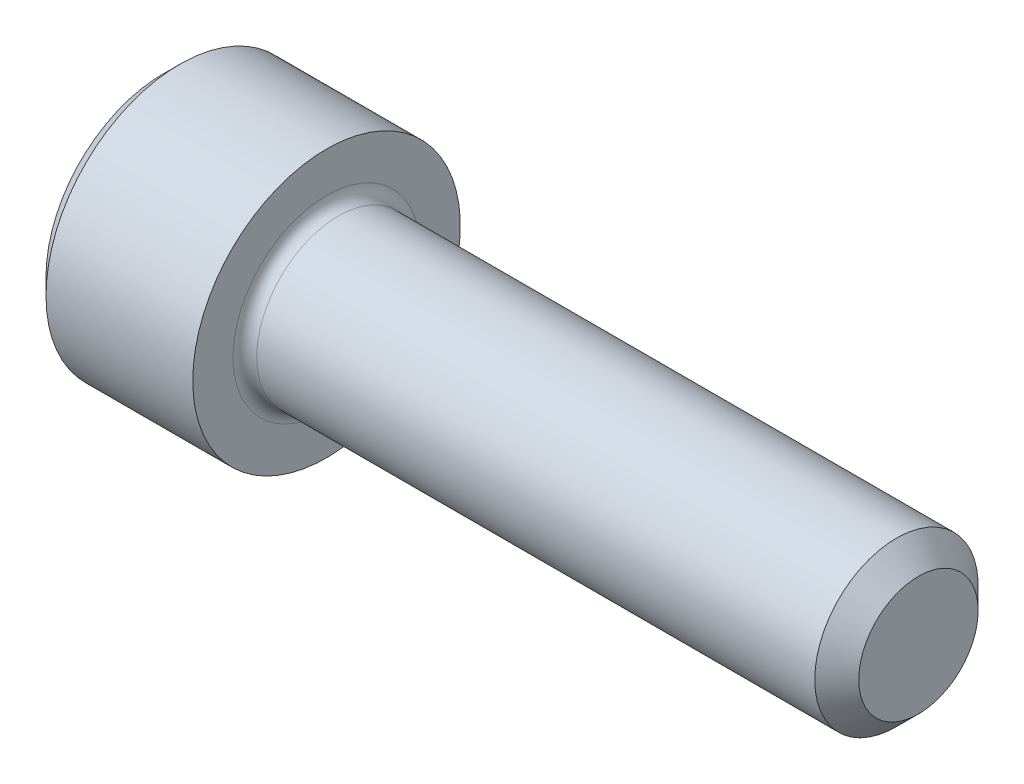
SolidWorks part; units mm, degrees
material "Alloy Steel"
ref_plane "Plane1" through (0, 0, 0) normal (0, 0, 1) x (1, 0, 0)
ref_plane "Plane2" through (0, 0, 0) normal (0, 1, 0) x (1, 0, 0)
ref_plane "Plane3" through (0, 0, 0) normal (1, 0, 0) x (0, 0, -1)
sketch "BodySke" plane through (0, 0, 0) normal (0, 0, 1) x (1, 0, 0)
  line L0 (0, 0) -> (0, 2.5146)
  line L1 (0.3556, 2.8702) -> (3.5052, 2.8702)
  line L2 (3.5052, 2.8702) -> (3.5052, 1.7526)
  line L3 (3.5052, 1.7526) -> (15.7328, 1.7526)
  line L4 (16.2052, 1.2802) -> (16.2052, 0)
  line L5 (16.2052, 0) -> (0, 0)
  line L6 (-31.75, 0) -> (127, 0) construction
  line L7 (0, 2.5146) -> (0.3556, 2.8702)
  line L8 (16.2052, 1.2802) -> (15.7328, 1.7526)
  line L9 (0, -2.5146) -> (0.3556, -2.8702) construction
  line L10 (16.2052, -1.2802) -> (15.7328, -1.7526) construction
  line L11 (4.2977, 9.525) -> (4.2977, 3.175) construction
  line L12 (3.5052, 9.525) -> (3.5052, 3.175) construction
  line L13 (-21.8948, 9.525) -> (-21.8948, 3.175) construction
  dimension "Diameter" = 3.5052
  dimension "Head_ht" = 3.5052
  dimension "Length" = 12.7
  dimension "Body_ch_ang" = 45
  dimension "Head_dia" = 5.7404
  dimension "Head_ch_ang" = 45
  dimension "Head_side_ht" = 3.1496
  dimension "Minor_dia" = 2.5603
  dimension "Advance" = 0.7925
  dimension "Thread_nom" = 12.7
  dimension "Thread_length" = 38.1
revolve "Base-Revolve" add sketch "BodySke"
cosmetic thread "ThreadCosmetic"
fillet "Fillet1" radius 0.254 1 edges at (3.5052, 0, 1.7526)
sketch "Sketch2" plane through (0, 0, 0) normal (0, 0, 1) x (1, 0, 0)
  line L0 (0, 1.3843) -> (1.6256, 1.3843)
  line L1 (1.6256, 1.3843) -> (2.4248, 0)
  line L2 (-31.75, 0) -> (127, 0) construction
  line L3 (2.4248, 0) -> (0, 0)
  line L4 (0, 0) -> (0, 1.3843)
  line L5 (0, 2.5146) -> (0, -2.5146) construction
  line L6 (0, 0) -> (47.625, 0) construction
  line L7 (3.5052, -2.8702) -> (3.5052, 2.8702) construction
  dimension "D1" = 1.3843
  dimension "D2" = 60
  dimension "Wall_thickness" = 1.8796
revolve "Hex-PreBroach" cut sketch "Sketch2" angle 360 about L6
sketch "Sketch3" plane through (0, 0, 0) normal (-1, 0, 0) x (0, 0.5, 0.866)
  line L0 (0.7992, 1.3843) -> (-0.7992, 1.3843)
  line L1 (-0.7992, 1.3843) -> (-1.5985, 0)
  line L2 (0.7992, 1.3843) -> (1.5985, 0)
  line L3 (0.7992, -1.3843) -> (1.5985, 0)
  line L4 (0.7992, -1.3843) -> (-0.7992, -1.3843)
  line L5 (-0.7992, -1.3843) -> (-1.5985, 0)
  dimension "D1" = 1.3843
  dimension "D2" = 1.3843
  dimension "Hex_size" = 2.7686
extrude "Hex" cut sketch "Sketch3" against normal blind 1.6256
sketch "Sketch4" plane through (0, 0, 0) normal (-1, 0, 0) x (0, 0, 1)
  line L0 (0, 0) -> (1.7399, 0)
  line L1 (0, 0) -> (6.1484, 3.5498) construction
  line L2 (0, 0) -> (0.8699, 1.5068)
  line L3 (1.4457, 0.3947) -> (1.6607, 0.5189)
  line L4 (1.0647, 1.0546) -> (1.2797, 1.1788)
  arc A0 (1.4457, 0.3947) -> (1.0647, 1.0546) centre (0, 0) ccw
  arc A1 (1.7399, 0) -> (1.6607, 0.5189) centre (0, 0) ccw
  arc A2 (0.8699, 1.5068) -> (1.2797, 1.1788) centre (0, 0) cw
  dimension "D1" = 30
  dimension "Spline_n_dim" = 2.9972
  dimension "Spline_m_dim" = 3.4798
  dimension "D2" = 60
  dimension "D3" = 0.381
  dimension "Spline_p_dim" = 0.762
extrude "Spline" [suppressed] cut sketch "Sketch4" against normal blind 1.6256
pattern_circular "CirPattern1" [suppressed] count 6 every 60
sketch "Sketch5" plane through (0, 0, 0) normal (0, 0, 1) x (1, 0, 0)
  line L0 (-31.75, 0) -> (127, 0) construction
  line L2 (0, 2.5146) -> (0, -2.5146) construction
  circle A0 centre (1.27, 0) radius 0.4445
  dimension "Drilled_hole_dia" = 0.889
  dimension "Drilled_hole_loc" = 1.27
extrude "Hole" [suppressed] cut sketch "Sketch5" against normal through all and the other way through all
pattern_circular "Drilled-4" [suppressed] count 2 every 60
pattern_circular "Drilled-6" [suppressed] count 3 every 60
sketch "ThdSchSke" plane through (0, 0, 0) normal (0, 0, 1) x (1, 0, 0)
  line L0 (4.2977, -1.2802) -> (3.9669, -1.7526)
  line L1 (4.2977, -1.2802) -> (4.6285, -1.7526)
  line L2 (4.6285, -1.7526) -> (4.6285, -2.1908)
  line L3 (-3.175, 0) -> (5.1513, 0) construction
  line L5 (4.6285, -2.1908) -> (3.9669, -2.1908)
  line L6 (3.9669, -2.1908) -> (3.9669, -1.7526)
  line L7 (0, 2.5146) -> (0, -2.5146) construction
  dimension "Thread_minor" = 2.5603
  dimension "Diameter" = 3.5052
  dimension "Start" = 4.2977
  dimension "SideAngle" = 55
  dimension "VeeAngle" = 70
  dimension "Overcut" = 4.3815
revolve "ThreadSchematic" [suppressed] cut sketch "ThdSchSke" angle 360 about L3
pattern_linear "ThdSchPat" [suppressed]
equation "\"D2@Sketch3\" = \"Hex_size@Sketch3\" / 2"
equation "\"D1@Sketch3\" = \"Hex_size@Sketch3\" / 2"
equation "\"D1@Sketch2\" = \"Hex_size@Sketch3\" / 2"
equation "\"D3@Sketch4\" = \"Spline_p_dim@Sketch4\" / 2"
equation "\"Thread_minor@ThreadCosmetic\"  =  \"Minor_dia@BodySke\""
equation "\"D2@CirPattern1\" = 360 / \"Num_teeth@CirPattern1\""
equation "\"Wall_thickness@Sketch2\" = \"Head_ht@BodySke\" - \"Key_eng@Hex\""
equation "\"Thread_length@ThreadCosmetic\" = ((sgn( (\"Length@BodySke\" - \"Advance@BodySke\" ) - \"Thread_nom@BodySke\" )-1)*( (\"Length@BodySke\" - \"Advance@BodySke\" ) - \"Thread_nom@BodySke\" ))/-2+ \"Thread_nom@BodySke\""
equation "\"Thread_minor@ThdSchSke\" = \"Minor_dia@BodySke\""
equation "\"Diameter@ThdSchSke\" = \"Diameter@BodySke\""
equation "\"Overcut@ThdSchSke\" = \"Diameter@BodySke\" * 1.25"
equation "\"Start@ThdSchSke\" = \"Head_ht@BodySke\" + \"Length@BodySke\" - \"Thread_length@ThreadCosmetic\"  '---Non-countersunk---"
equation "\"Num_threads@ThdSchPat\" = int( \"Thread_length@ThreadCosmetic\" / \"Advance@BodySke\" + 0.999 )  + 1"
equation "\"Advance@ThdSchPat\" = \"Thread_length@ThreadCosmetic\" /  (\"Num_threads@ThdSchPat\" - 1) 'relax it"
equation "\"Num_threads@ThdSchPat\" = \"Num_threads@ThdSchPat\" - sgn( \"Num_threads@ThdSchPat\" - 1) '---chamfered tips only---"
